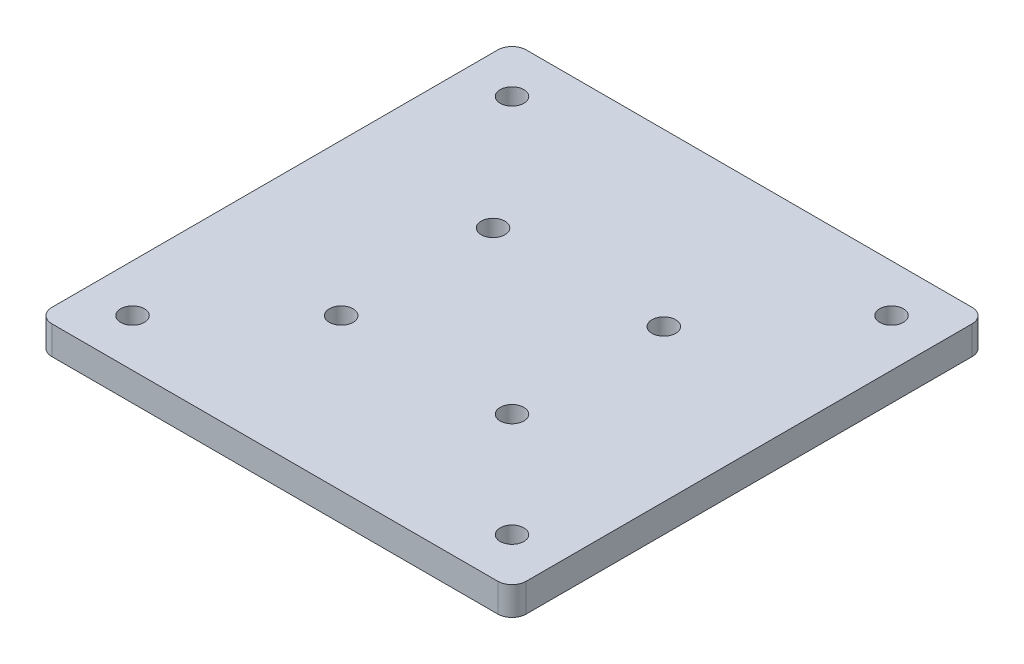
SolidWorks part; units mm, degrees
ref_plane "Front Plane" through (0, 0, 0) normal (0, 0, 1) x (1, 0, 0)
ref_plane "Top Plane" through (0, 0, 0) normal (0, 1, 0) x (1, 0, 0)
ref_plane "Right Plane" through (0, 0, 0) normal (1, 0, 0) x (0, 0, -1)
sketch "Sketch1" plane through (0, 0, 0) normal (0, 1, 0) x (1, 0, 0)
  line L1 (-10, 90) -> (90, 90)
  line L2 (-10, 90) -> (-10, -10)
  line L3 (-10, -10) -> (90, -10)
  line L4 (90, 90) -> (90, -10)
  circle A0 centre (0, 0) radius 2.5
  circle A1 centre (80, 0) radius 2.5
  circle A2 centre (0, 80) radius 2.5
  circle A3 centre (80, 80) radius 2.5
  circle A4 centre (0, 32) radius 2.5 [skipped]
  circle A5 centre (80, 32) radius 2.5 [skipped]
  circle A6 centre (22, 22) radius 2.5
  circle A7 centre (58, 22) radius 2.5
  circle A8 centre (22, 54) radius 2.5
  circle A9 centre (58, 54) radius 2.5
  dimension "D1" = 5
  dimension "D9" = 5
  dimension "D10" = 5
  dimension "D12" = 10
  dimension "D13" = 100
  dimension "D14" = 10
  dimension "D15" = 5
  dimension "D16" = 5
  dimension "D17" = 5
  dimension "D18" = 5
  dimension "D22" = 36
  dimension "D21" = 32
  dimension "D23" = 32
  dimension "D24" = 32
  dimension "D8" = 90
  dimension "D11" = 90
  dimension "D4" = 10
  dimension "D5" = 10
  dimension "D6" = 10
  dimension "D7" = 100
  dimension "D19" = 32
  dimension "D20" = 36
  dimension "D2" = 2
  dimension "D3" = 2
extrude "Boss-Extrude1" add sketch "Sketch1" along normal blind 6
fillet "Fillet1" radius 3 2 edges at (-10, 3, 10) (90, 3, 10)
fillet "Fillet2" radius 3 2 edges at (-10, 3, -90) (90, 3, -90)
